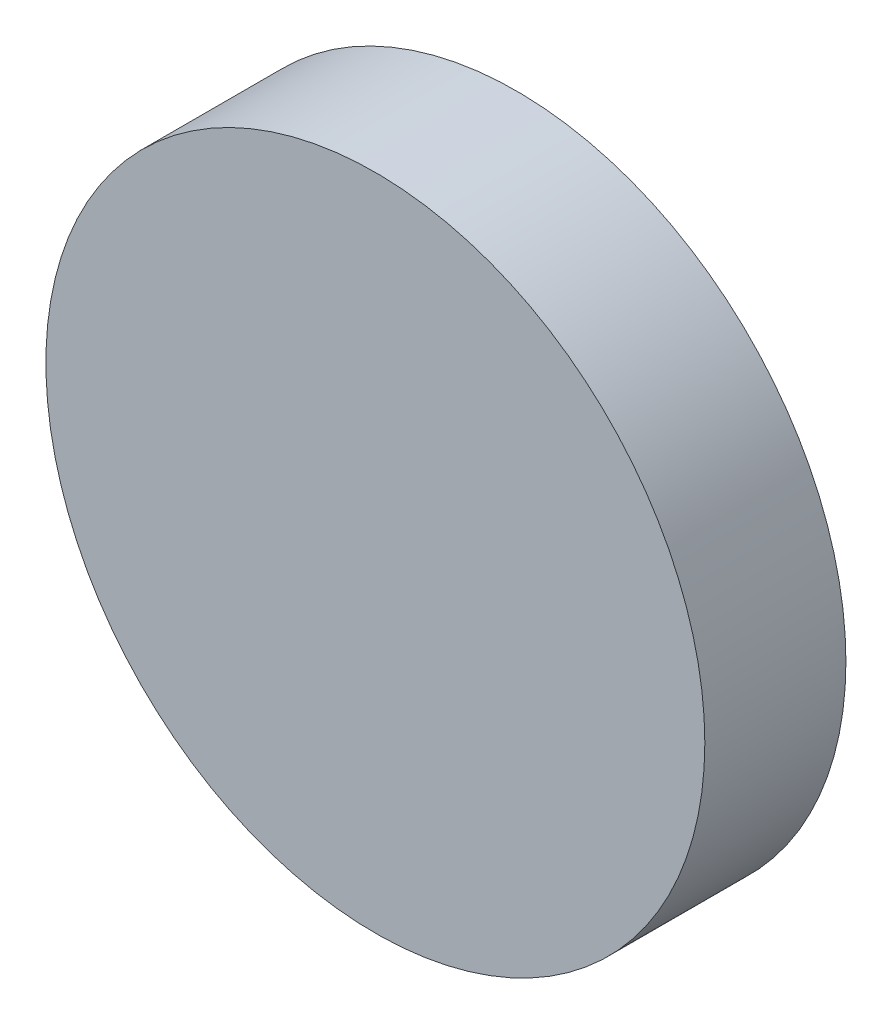
SolidWorks part; units mm, degrees
material "Plain Carbon Steel"
ref_plane "Front" through (0, 0, 0) normal (0, 0, 1) x (1, 0, 0)
ref_plane "Top" through (0, 0, 0) normal (0, 1, 0) x (1, 0, 0)
ref_plane "Right" through (0, 0, 0) normal (1, 0, 0) x (0, 0, -1)
sketch "Sketch1" plane through (0, 0, 0) normal (0, 0, 1) x (1, 0, 0)
  circle A0 centre (-17.6985, 13.2253) radius 50.8
  circle A1 centre (-17.6985, 13.2253) radius 53.3821
  dimension "D1" = 101.6
extrude "Boss-Extrude1" add sketch "Sketch1" along normal blind 20.32
sketch "Sketch2" plane through (0, 0, 20.32) normal (0, 0, 1) x (1, 0, 0)
  line L0 (-17.6985, 66.6074) -> (-17.6985, -40.1569) construction
  circle A0 centre (-17.6985, 13.2253) radius 53.3821 construction
  circle A1 centre (-17.6985, 13.2253) radius 53.3821
extrude "Boss-Extrude2" add sketch "Sketch2" along normal blind 2.54
